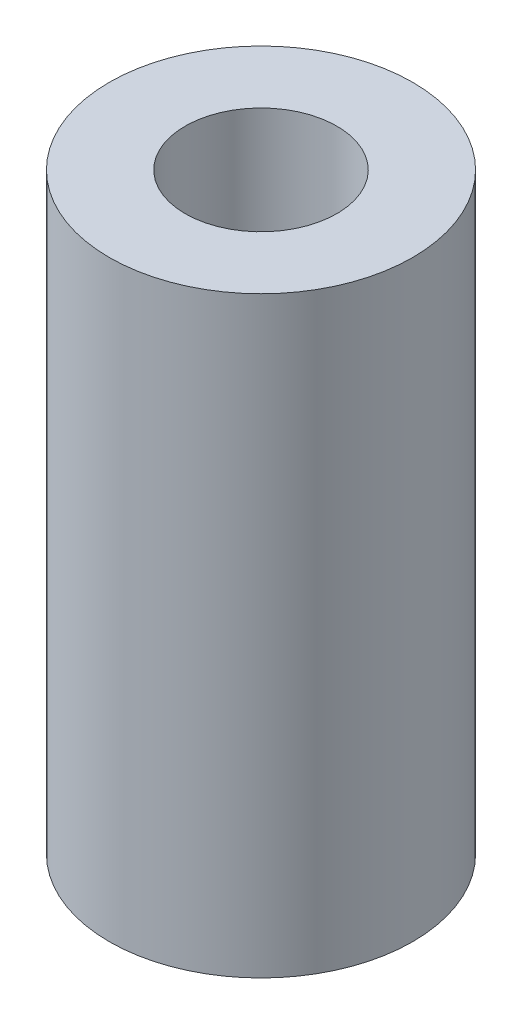
SolidWorks part; units mm, degrees
ref_plane "Front Plane" through (0, 0, 0) normal (0, 0, 1) x (1, 0, 0)
ref_plane "Top Plane" through (0, 0, 0) normal (0, 1, 0) x (1, 0, 0)
ref_plane "Right Plane" through (0, 0, 0) normal (1, 0, 0) x (0, 0, -1)
sketch "Sketch1" plane through (0, 0, 0) normal (0, 1, 0) x (1, 0, 0)
  circle A0 centre (0, 0) radius 6.35
  dimension "D1" = 12.7
extrude "Boss-Extrude1" add sketch "Sketch1" along normal blind 24.8
sketch "Sketch2" plane through (0, 24.8, 0) normal (0, 1, 0) x (1, 0, 0)
  circle A0 centre (0, 0) radius 3.175
  dimension "D1" = 6.35
extrude "Cut-Extrude1" cut sketch "Sketch2" against normal blind 18.6
sketch "Sketch3" plane through (0, 0, 0) normal (0, -1, 0) x (1, 0, 0)
  circle A0 centre (0, 0) radius 14.2572
